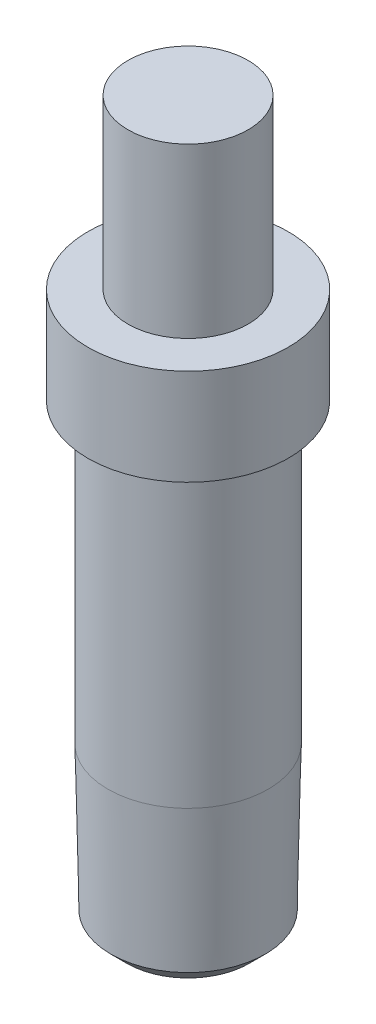
SolidWorks part; units mm, degrees
ref_plane "Front Plane" through (0, 0, 0) normal (0, 0, 1) x (1, 0, 0)
ref_plane "Top Plane" through (0, 0, 0) normal (0, 1, 0) x (1, 0, 0)
ref_plane "Right Plane" through (0, 0, 0) normal (1, 0, 0) x (0, 0, -1)
sketch "Sketch2" plane through (0, 0, 0) normal (0, 1, 0) x (1, 0, 0)
  circle A0 centre (0, 0) radius 1.25
  dimension "D1" = 2.5
extrude "Boss-Extrude1" add sketch "Sketch2" along normal blind 9
sketch "Sketch4" plane through (0, 0, 0) normal (0, 0, 1) x (1, 0, 0)
  line L0 (0, 9) -> (0, 0.1536) construction
  line L1 (1.25, 9) -> (-1.25, 9) construction
  line L2 (0.75, 9) -> (0.75, 6.9)
  line L3 (0.75, 6.9) -> (1.25, 6.9)
  line L4 (1.25, 0) -> (1.25, 9) construction
  line L5 (1.25, 6.9) -> (1.25, 5.7)
  line L6 (1.25, 5.7) -> (1, 5.7)
  line L7 (1, 5.7) -> (1, 2)
  line L8 (1, 2) -> (0.9639, 0.2)
  line L9 (0.75, 9) -> (1.75, 9)
  line L11 (0.9639, 0.2) -> (0.7639, 0)
  line L12 (-1.25, 0) -> (1.25, 0) construction
  line L13 (0.7639, 0) -> (1.75, 0)
  line L15 (1.75, 0) -> (1.75, 9)
  line L16 (1.75, 0) -> (1.75, 9)
  dimension "D1" = 3.3
  dimension "D2" = 1.2
  dimension "D3" = 1.5
  dimension "D4" = 2
  dimension "D5" = 2
  dimension "D6" = 0.2
  dimension "D7" = 45
  dimension "D8" = 1.15
  dimension "D9" = 0.5
revolve "Cut-Revolve1" cut sketch "Sketch4" angle 360 about L0
